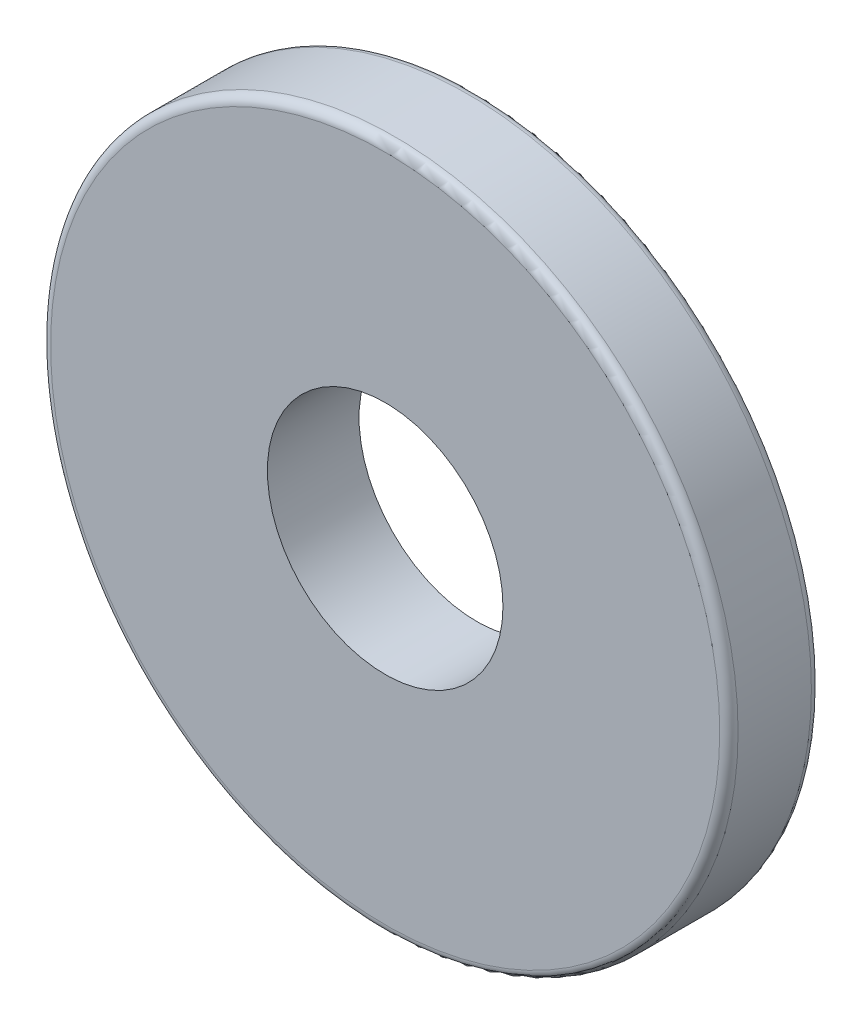
SolidWorks part; units mm, degrees
ref_plane "Front Plane" through (0, 0, 0) normal (0, 0, 1) x (1, 0, 0)
ref_plane "Top Plane" through (0, 0, 0) normal (0, 1, 0) x (1, 0, 0)
ref_plane "Right Plane" through (0, 0, 0) normal (1, 0, 0) x (0, 0, -1)
sketch "Sketch2" plane through (0, 0, 0) normal (0, 0, 1) x (1, 0, 0)
  circle A0 centre (0, 0) radius 3.2639
  circle A1 centre (0, 0) radius 9.525
  dimension "D1" = 6.5278
  dimension "D2" = 19.05
extrude "Boss-Extrude1" add sketch "Sketch2" along normal blind 2.54
fillet "Fillet1" radius 0.254 2 edges at (9.525, 0, 0) (9.525, 0, 2.54)
